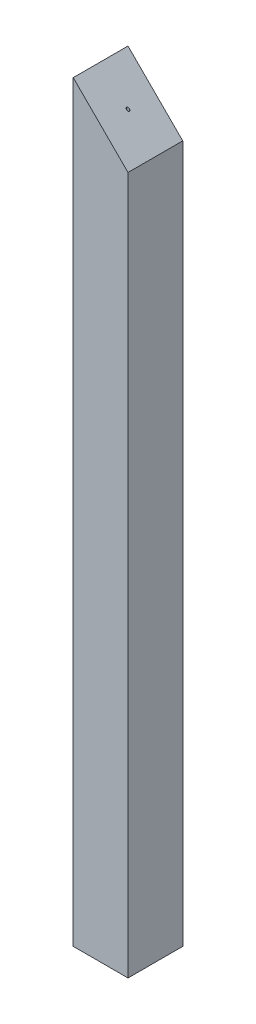
SolidWorks part; units mm, degrees
ref_plane "Front Plane" through (0, 0, 0) normal (0, 0, 1) x (1, 0, 0)
ref_plane "Top Plane" through (0, 0, 0) normal (0, 1, 0) x (1, 0, 0)
ref_plane "Right Plane" through (0, 0, 0) normal (1, 0, 0) x (0, 0, -1)
sketch "Sketch1" plane through (0, 0, 0) normal (0, 1, 0) x (1, 0, 0)
  line L1 (-12.7, 12.7) -> (12.7, 12.7)
  line L2 (-12.7, 12.7) -> (-12.7, -12.7)
  line L3 (-12.7, -12.7) -> (12.7, -12.7)
  line L4 (12.7, 12.7) -> (12.7, -12.7)
  line L5 (-12.7, 12.7) -> (12.7, -12.7) construction
  line L6 (-12.7, -12.7) -> (12.7, 12.7) construction
  point P0 (0, 0)
  dimension "D1" = 25.4
  dimension "D2" = 25.4
extrude "Boss-Extrude1" add sketch "Sketch1" along normal mid plane 348.97
hole_wizard "#0-80 Tapped Hole1" positions "Sketch2" profile "Sketch3" tap size "#0-80" standard "ANSI Inch"
sketch "Sketch2" plane through (0, -174.485, 0) normal (0, -1, 0) x (-1, 0, 0)
  point P0 (0, 0)
sketch "Sketch3" plane through (0, -174.485, 0) normal (1, 0, 0) x (0, 0, -1)
  line L0 (0, 0) -> (0, 20.3579)
  line L1 (0, 20.3579) -> (0.5956, 20)
  line L2 (0.5956, 20) -> (0.5956, 0.7683)
  line L3 (0.5956, 0.7683) -> (1.5113, 0)
  line L5 (1.5113, 0) -> (0, 0)
  line L6 (-0.5956, 0.7683) -> (-1.5113, 0) construction
  line L10 (0, 20.3579) -> (-0.5956, 20) construction
  line L11 (0, -6.35) -> (0, 107.95) construction
  dimension "Tap Drill Dia." = 1.1913
  dimension "Tap Drill Depth" = 20
  dimension "Near C'Sink Dia." = 3.0226
  dimension "Near C'Sink Angle" = 100
  dimension "Drill Angle" = 118
cosmetic thread "Hole Thread1" parameters "D1"=10, "D2"=1.524
mirror "Mirror1" about plane through (0, 0, 0) normal (0, 1, 0) of "#0-80 Tapped Hole1"
sketch "Sketch4" plane through (0, 0, 0) normal (0, 0, 1) x (1, 0, 0)
  line L0 (12.7, 174.485) -> (-12.7, 174.485)
  line L1 (-12.7, 174.485) -> (12.7, 149.085)
  line L2 (12.7, 174.485) -> (12.7, -174.485) construction
  line L3 (12.7, 149.085) -> (12.7, 174.485)
  line L4 (-12.7, 174.485) -> (-12.7, -174.485) construction
  dimension "D1" = 45
extrude "Cut-Extrude1" cut sketch "Sketch4" against normal through all both and the other way through all
